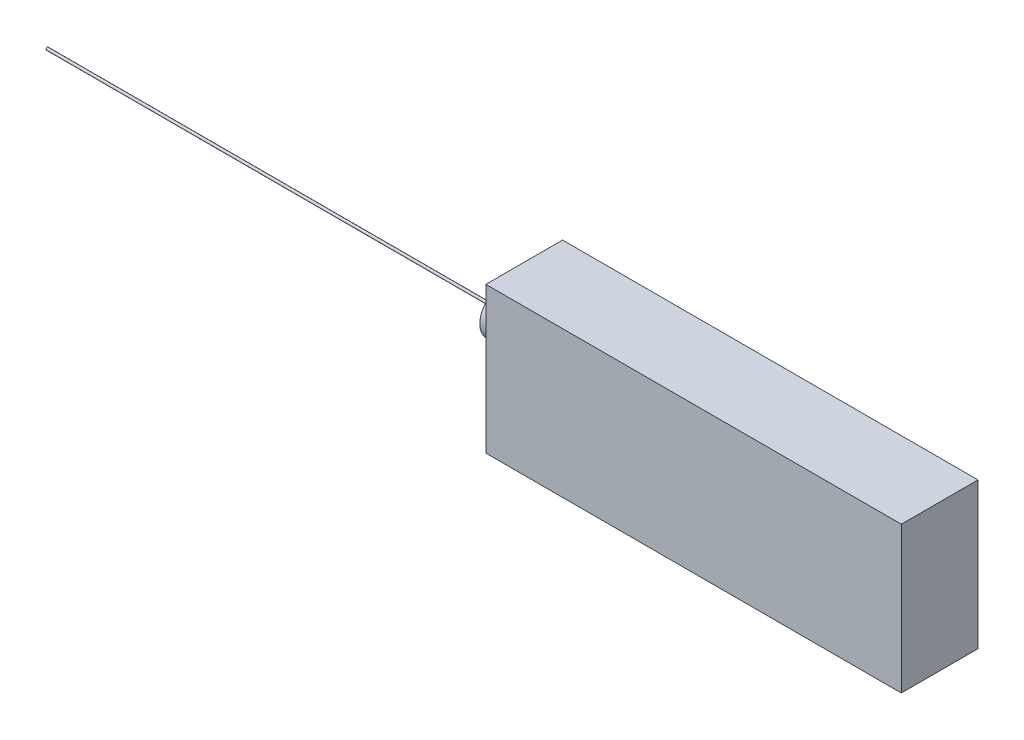
SolidWorks part; units mm, degrees
ref_plane "Front Plane" through (0, 0, 0) normal (0, 0, 1) x (1, 0, 0)
ref_plane "Top Plane" through (0, 0, 0) normal (0, 1, 0) x (1, 0, 0)
ref_plane "Right Plane" through (0, 0, 0) normal (1, 0, 0) x (0, 0, -1)
sketch "Sketch1" plane through (0, 0, 0) normal (0, 1, 0) x (1, 0, 0)
  line L1 (-162.5, 30) -> (162.5, 30)
  line L2 (-162.5, 30) -> (-162.5, -30)
  line L3 (-162.5, -30) -> (162.5, -30)
  line L4 (162.5, 30) -> (162.5, -30)
  line L5 (-162.5, 30) -> (162.5, -30) construction
  line L6 (-162.5, -30) -> (162.5, 30) construction
  point P0 (0, 0)
  dimension "D1" = 325
  dimension "D2" = 60
extrude "Boss-Extrude1" add sketch "Sketch1" against normal blind 114.37
sketch "Sketch2" plane through (-162.5, 0, 0) normal (-1, 0, 0) x (0, 0, 1)
  line L0 (-30, -114.37) -> (-30, 0) construction
  line L1 (-30, -114.37) -> (30, -114.37) construction
  circle A0 centre (-7.5, -49.37) radius 17.2387
  dimension "D1" = 22.5
  dimension "D2" = 65
extrude "Boss-Extrude2" add sketch "Sketch2" along normal blind 25
sketch "Sketch3" plane through (-187.5, 0, 0) normal (-1, 0, 0) x (0, 0, 1)
  circle A0 centre (-7.5, -49.37) radius 1
  dimension "D1" = 2
extrude "Boss-Extrude3" add sketch "Sketch3" along normal blind 355.6
